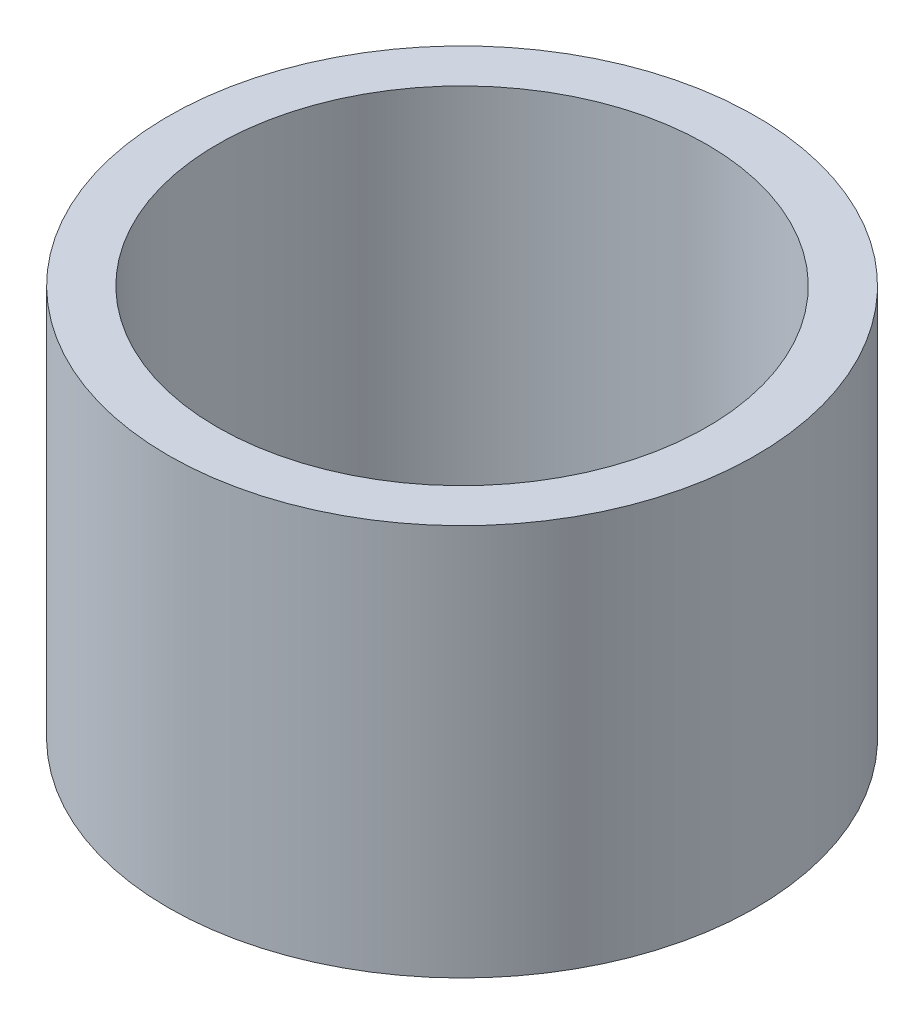
SolidWorks part; units mm, degrees
ref_plane "Front Plane" through (0, 0, 0) normal (0, 0, 1) x (1, 0, 0)
ref_plane "Top Plane" through (0, 0, 0) normal (0, 1, 0) x (1, 0, 0)
ref_plane "Right Plane" through (0, 0, 0) normal (1, 0, 0) x (0, 0, -1)
sketch "Sketch16" plane through (0, 0, 0) normal (1, 0, 0) x (0, 0, -1)
  line L0 (0, 0) -> (60, 0)
  line L1 (60, 0) -> (60, 80)
  line L2 (60, 80) -> (0, 80)
  line L3 (0, 80) -> (0, 0)
  dimension "D1" = 80
  dimension "D2" = 60
revolve "Revolve4" add sketch "Sketch16" angle 360 about L3
sketch "Sketch17" plane through (0, 80, 0) normal (0, 1, 0) x (1, 0, 0)
  circle A0 centre (0, 0) radius 50
  dimension "D1" = 100
extrude "Cut-Extrude3" cut sketch "Sketch17" against normal blind 100
